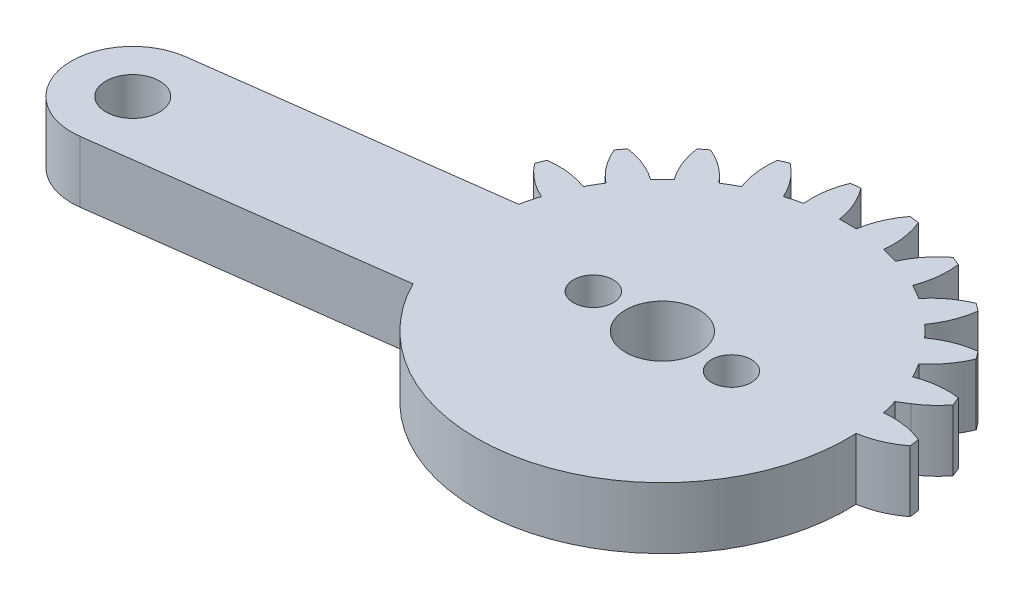
SolidWorks part; units mm, degrees
ref_plane "Front Plane" through (0, 0, 0) normal (0, 0, 1) x (1, 0, 0)
ref_plane "Top Plane" through (0, 0, 0) normal (0, 1, 0) x (1, 0, 0)
ref_plane "Right Plane" through (0, 0, 0) normal (1, 0, 0) x (0, 0, -1)
sketch "Sketch1" plane through (0, 0, 0) normal (0, 1, 0) x (1, 0, 0)
  line L0 (20.6437, 4) -> (2.0816, 4)
  line L1 (2.0816, -4) -> (20.6437, -4)
  arc A0 (2.0816, 4) -> (3.5217, 5.3071) centre (-0.7683, 8.5867) ccw
  arc A1 (3.5217, 5.3071) -> (3.2829, 5.8838) centre (-10.1063, 0) ccw
  arc A2 (3.2829, 5.8838) -> (0.6271, 5.5703) centre (2.5684, 0.5313) ccw
  arc A3 (0.6271, 5.5703) -> (0.0844, 6.5103) centre (-10.1063, 0) ccw
  arc A4 (0.0844, 6.5103) -> (1.6838, 8.6535) centre (-3.3089, 10.711) ccw
  arc A5 (1.6838, 8.6535) -> (1.3038, 9.1487) centre (-10.1063, 0) ccw
  arc A6 (1.3038, 9.1487) -> (-1.1803, 8.1585) centre (1.999, 3.7936) ccw
  arc A7 (-1.1803, 8.1585) -> (-1.9479, 8.926) centre (-10.1063, 0) ccw
  arc A8 (-1.9479, 8.926) -> (-0.9576, 11.4102) centre (-6.3127, 12.1053) ccw
  arc A9 (-0.9576, 11.4102) -> (-1.4528, 11.7901) centre (-10.1063, 0) ccw
  arc A10 (-1.4528, 11.7901) -> (-3.596, 10.1907) centre (0.6046, 6.7975) ccw
  arc A11 (-3.596, 10.1907) -> (-4.5361, 10.7334) centre (-10.1063, 0) ccw
  arc A12 (-4.5361, 10.7334) -> (-4.2225, 13.3892) centre (-9.5751, 12.6747) ccw
  arc A13 (-4.2225, 13.3892) -> (-4.7992, 13.6281) centre (-10.1063, 0) ccw
  arc A14 (-4.7992, 13.6281) -> (-6.4554, 11.5285) centre (-1.5196, 9.3381) ccw
  arc A15 (-6.4554, 11.5285) -> (-7.5039, 11.8094) centre (-10.1063, 0) ccw
  arc A16 (-7.5039, 11.8094) -> (-7.8884, 14.4558) centre (-12.8736, 12.3803) ccw
  arc A17 (-7.8884, 14.4558) -> (-8.5072, 14.5373) centre (-10.1063, 0) ccw
  arc A18 (-8.5072, 14.5373) -> (-9.5636, 12.0806) centre (-4.2291, 11.2423) ccw
  arc A19 (-9.5636, 12.0806) -> (-10.6491, 12.0806) centre (-10.1063, 0) ccw
  arc A20 (-10.6491, 12.0806) -> (-11.7054, 14.5373) centre (-15.9836, 11.2423) ccw
  arc A21 (-11.7054, 14.5373) -> (-12.3243, 14.4558) centre (-10.1063, 0) ccw
  arc A22 (-12.3243, 14.4558) -> (-12.7088, 11.8094) centre (-7.3391, 12.3803) ccw
  arc A23 (-12.7088, 11.8094) -> (-13.7573, 11.5285) centre (-10.1063, 0) ccw
  arc A24 (-13.7573, 11.5285) -> (-15.4135, 13.6281) centre (-18.6931, 9.3381) ccw
  arc A25 (-15.4135, 13.6281) -> (-15.9901, 13.3892) centre (-10.1063, 0) ccw
  arc A26 (-15.9901, 13.3892) -> (-15.6766, 10.7334) centre (-10.6376, 12.6747) ccw
  arc A27 (-15.6766, 10.7334) -> (-16.6166, 10.1907) centre (-10.1063, 0) ccw
  arc A28 (-16.6166, 10.1907) -> (-18.7599, 11.7901) centre (-20.8173, 6.7975) ccw
  arc A29 (-18.7599, 11.7901) -> (-19.255, 11.4102) centre (-10.1063, 0) ccw
  arc A30 (-19.255, 11.4102) -> (-18.2648, 8.926) centre (-13.9, 12.1053) ccw
  arc A31 (-18.2648, 8.926) -> (-19.0324, 8.1585) centre (-10.1063, 0) ccw
  arc A32 (-19.0324, 8.1585) -> (-21.5165, 9.1487) centre (-22.2117, 3.7936) ccw
  arc A33 (-21.5165, 9.1487) -> (-21.8965, 8.6535) centre (-10.1063, 0) ccw
  arc A34 (-21.8965, 8.6535) -> (-20.2971, 6.5103) centre (-16.9038, 10.711) ccw
  arc A35 (-20.2971, 6.5103) -> (-20.8398, 5.5703) centre (-10.1063, 0) ccw
  arc A36 (-20.8398, 5.5703) -> (-23.4956, 5.8838) centre (-22.7811, 0.5313) ccw
  arc A37 (-23.4956, 5.8838) -> (-23.7344, 5.3071) centre (-10.1063, 0) ccw
  arc A38 (-23.7344, 5.3071) -> (-21.6348, 3.6509) centre (-19.4444, 8.5867) ccw
  arc A39 (-21.6348, 3.6509) -> (-21.9157, 2.6025) centre (-10.1063, 0) ccw
  arc A40 (-21.9157, 2.6025) -> (-24.5622, 2.2179) centre (-22.4867, -2.7673) ccw
  arc A41 (-24.5622, 2.2179) -> (-24.6437, 1.5991) centre (-10.1063, 0) ccw
  arc A42 (-24.6437, 1.5991) -> (-22.1869, 0.5427) centre (-21.3486, 5.8773) ccw
  arc A43 (-22.1869, 0.5427) -> (-22.1869, -0.5427) centre (-10.1063, 0) ccw
  arc A44 (-22.1869, -0.5427) -> (-24.6437, -1.5991) centre (-21.3486, -5.8773) ccw
  arc A45 (-24.6437, -1.5991) -> (-24.5622, -2.2179) centre (-10.1063, 0) ccw
  arc A46 (-24.5622, -2.2179) -> (-21.9157, -2.6025) centre (-22.4867, 2.7673) ccw
  arc A47 (-21.9157, -2.6025) -> (-21.6348, -3.6509) centre (-10.1063, 0) ccw
  arc A48 (-21.6348, -3.6509) -> (-23.7344, -5.3071) centre (-19.4444, -8.5867) ccw
  arc A49 (-23.7344, -5.3071) -> (-23.4956, -5.8838) centre (-10.1063, 0) ccw
  arc A50 (-23.4956, -5.8838) -> (-20.8398, -5.5703) centre (-22.7811, -0.5313) ccw
  arc A51 (-20.8398, -5.5703) -> (-20.2971, -6.5103) centre (-10.1063, 0) ccw
  arc A52 (-20.2971, -6.5103) -> (-21.8965, -8.6535) centre (-16.9038, -10.711) ccw
  arc A53 (-21.8965, -8.6535) -> (-21.5165, -9.1487) centre (-10.1063, 0) ccw
  arc A54 (-21.5165, -9.1487) -> (-19.0324, -8.1585) centre (-22.2117, -3.7936) ccw
  arc A55 (-19.0324, -8.1585) -> (-18.2648, -8.926) centre (-10.1063, 0) ccw
  arc A56 (-18.2648, -8.926) -> (-19.255, -11.4102) centre (-13.9, -12.1053) ccw
  arc A57 (-19.255, -11.4102) -> (-18.7599, -11.7901) centre (-10.1063, 0) ccw
  arc A58 (-18.7599, -11.7901) -> (-16.6166, -10.1907) centre (-20.8173, -6.7975) ccw
  arc A59 (-16.6166, -10.1907) -> (-15.6766, -10.7334) centre (-10.1063, 0) ccw
  arc A60 (-15.6766, -10.7334) -> (-15.9901, -13.3892) centre (-10.6376, -12.6747) ccw
  arc A61 (-15.9901, -13.3892) -> (-15.4135, -13.6281) centre (-10.1063, 0) ccw
  arc A62 (-15.4135, -13.6281) -> (-13.7573, -11.5285) centre (-18.6931, -9.3381) ccw
  arc A63 (-13.7573, -11.5285) -> (-12.7088, -11.8094) centre (-10.1063, 0) ccw
  arc A64 (-12.7088, -11.8094) -> (-12.3243, -14.4558) centre (-7.3391, -12.3803) ccw
  arc A65 (-12.3243, -14.4558) -> (-11.7054, -14.5373) centre (-10.1063, 0) ccw
  arc A66 (-11.7054, -14.5373) -> (-10.6491, -12.0806) centre (-15.9836, -11.2423) ccw
  arc A67 (-10.6491, -12.0806) -> (-9.5636, -12.0806) centre (-10.1063, 0) ccw
  arc A68 (-9.5636, -12.0806) -> (-8.5072, -14.5373) centre (-4.2291, -11.2423) ccw
  arc A69 (-8.5072, -14.5373) -> (-7.8884, -14.4558) centre (-10.1063, 0) ccw
  arc A70 (-7.8884, -14.4558) -> (-7.5039, -11.8094) centre (-12.8736, -12.3803) ccw
  arc A71 (-7.5039, -11.8094) -> (-6.4554, -11.5285) centre (-10.1063, 0) ccw
  arc A72 (-6.4554, -11.5285) -> (-4.7992, -13.6281) centre (-1.5196, -9.3381) ccw
  arc A73 (-4.7992, -13.6281) -> (-4.2225, -13.3892) centre (-10.1063, 0) ccw
  arc A74 (-4.2225, -13.3892) -> (-4.5361, -10.7334) centre (-9.5751, -12.6747) ccw
  arc A75 (-4.5361, -10.7334) -> (-3.596, -10.1907) centre (-10.1063, 0) ccw
  arc A76 (-3.596, -10.1907) -> (-1.4528, -11.7901) centre (0.6046, -6.7975) ccw
  arc A77 (-1.4528, -11.7901) -> (-0.9576, -11.4102) centre (-10.1063, 0) ccw
  arc A78 (-0.9576, -11.4102) -> (-1.9479, -8.926) centre (-6.3127, -12.1053) ccw
  arc A79 (-1.9479, -8.926) -> (-1.1803, -8.1585) centre (-10.1063, 0) ccw
  arc A80 (-1.1803, -8.1585) -> (1.3038, -9.1487) centre (1.999, -3.7936) ccw
  arc A81 (1.3038, -9.1487) -> (1.6838, -8.6535) centre (-10.1063, 0) ccw
  arc A82 (1.6838, -8.6535) -> (0.0844, -6.5103) centre (-3.3089, -10.711) ccw
  arc A83 (0.0844, -6.5103) -> (0.6271, -5.5703) centre (-10.1063, 0) ccw
  arc A84 (0.6271, -5.5703) -> (3.2829, -5.8838) centre (2.5684, -0.5313) ccw
  arc A85 (3.2829, -5.8838) -> (3.5217, -5.3071) centre (-10.1063, 0) ccw
  arc A86 (3.5217, -5.3071) -> (2.0816, -4) centre (-0.7683, -8.5867) ccw
  arc A87 (20.6437, -4) -> (20.6437, 4) centre (20.6437, 0) ccw
  circle A88 centre (-10.1063, 0) radius 1.5
  circle A89 centre (20.6437, 0) radius 1.5
  dimension "D1" = 3
  dimension "D2" = 3
extrude "Boss-Extrude1" add sketch "Sketch1" along normal blind 4
sketch "Sketch3" plane through (0, 4, 0) normal (0, 1, 0) x (1, 0, 0)
  line L0 (-10.1063, 0) -> (-40.8563, 0) construction
  line L1 (-10.1063, 0) -> (-40.5933, -4.0137)
  line L2 (-10.6284, 3.9658) -> (-41.1154, -0.0479)
  line L3 (-9.5842, -3.9658) -> (-40.0712, -7.9795)
  line L4 (-10.1063, 0) -> (-4.5096, 13.5117) construction
  line L5 (-10.1063, 0) -> (-8.1974, 14.4999) construction
  circle A0 centre (-10.1063, 0) radius 1.5
  circle A1 centre (20.6437, 0) radius 1.5 construction
  circle A2 centre (20.6437, 0) radius 1.5
  circle A3 centre (-40.5933, -4.0137) radius 1.75
  circle A4 centre (-40.5933, -4.0137) radius 4
  circle A5 centre (-10.1063, 0) radius 4
  arc A6 (-4.2225, 13.3892) -> (-4.7992, 13.6281) centre (-10.1063, 0) ccw construction
  arc A7 (-7.8884, 14.4558) -> (-8.5072, 14.5373) centre (-10.1063, 0) ccw construction
  dimension "D2" = 3
  dimension "D5" = 3.5
  dimension "D6" = 8
  dimension "D7" = 8
  dimension "D1" = 30.75
  dimension "D4" = 7.5
extrude "Boss-Extrude2" add sketch "Sketch3" against normal blind 4
sketch "Sketch4" plane through (0, 4, 0) normal (0, 1, 0) x (1, 0, 0)
  line L0 (20.6437, 4) -> (2.0816, 4) construction
  line L1 (2.0816, -4) -> (20.6437, -4) construction
  line L2 (20.6437, 4) -> (2.0816, 4)
  line L3 (2.0816, -4) -> (20.6437, -4)
  line L4 (2.0816, 4) -> (1.4381, 3.6001)
  line L5 (-21.6245, -5.5509) -> (-20.8986, -5.4553)
  line L6 (-10.1063, 0) -> (0.0844, 6.5103) construction
  line L7 (-10.1063, 0) -> (1.9742, 0.5427) construction
  line L8 (-24.5755, 2.1296) -> (-41.1154, -0.0479)
  line L9 (-40.0712, -7.9795) -> (-23.5312, -5.8019)
  line L10 (2.0816, -4) -> (20.6437, -4)
  line L11 (20.6437, 4) -> (2.0816, 4)
  line L12 (-21.9429, 2.4762) -> (-41.1154, -0.0479)
  line L13 (-40.0712, -7.9795) -> (-21.6245, -5.5509)
  line L14 (2.0816, -4) -> (20.6437, -4)
  line L15 (20.6437, 4) -> (2.0816, 4)
  circle A0 centre (-10.1063, 0) radius 12.0927
  arc A1 (3.2829, 5.8838) -> (0.6271, 5.5703) centre (2.5684, 0.5313) ccw construction
  arc A2 (3.5217, 5.3071) -> (3.2829, 5.8838) centre (-10.1063, 0) ccw construction
  arc A3 (2.0816, 4) -> (3.5217, 5.3071) centre (-0.7683, 8.5867) ccw construction
  arc A4 (20.6437, -4) -> (20.6437, 4) centre (20.6437, 0) ccw construction
  arc A5 (3.5217, -5.3071) -> (2.0816, -4) centre (-0.7683, -8.5867) ccw construction
  arc A6 (3.2829, -5.8838) -> (3.5217, -5.3071) centre (-10.1063, 0) ccw construction
  arc A7 (0.6271, -5.5703) -> (3.2829, -5.8838) centre (2.5684, -0.5313) ccw construction
  arc A8 (3.2829, 5.8838) -> (0.6271, 5.5703) centre (2.5684, 0.5313) ccw
  arc A9 (3.5217, 5.3071) -> (3.2829, 5.8838) centre (-10.1063, 0) ccw
  arc A10 (2.0816, 4) -> (3.5217, 5.3071) centre (-0.7683, 8.5867) ccw
  arc A11 (20.6437, -4) -> (20.6437, 4) centre (20.6437, 0) ccw
  arc A12 (3.5217, -5.3071) -> (2.0816, -4) centre (-0.7683, -8.5867) ccw
  arc A13 (3.2829, -5.8838) -> (3.5217, -5.3071) centre (-10.1063, 0) ccw
  arc A14 (0.6271, -5.5703) -> (3.2829, -5.8838) centre (2.5684, -0.5313) ccw
  arc A15 (1.9742, 0.5427) -> (4.431, 1.5991) centre (1.1359, 5.8773) ccw
  arc A16 (4.3495, 2.2179) -> (1.7031, 2.6025) centre (2.274, -2.7673) ccw
  arc A17 (4.431, 1.5991) -> (4.3495, 2.2179) centre (-10.1063, 0) ccw
  arc A95 (-21.6348, 3.6509) -> (-21.9157, 2.6025) centre (-10.1063, 0) ccw
  arc A96 (-41.1154, -0.0479) -> (-40.0712, -7.9795) centre (-40.5933, -4.0137) ccw
  arc A97 (-20.2971, -6.5103) -> (-21.8965, -8.6535) centre (-16.9038, -10.711) ccw
  arc A98 (-21.8965, -8.6535) -> (-21.5165, -9.1487) centre (-10.1063, 0) ccw
  arc A99 (-21.5165, -9.1487) -> (-19.0324, -8.1585) centre (-22.2117, -3.7936) ccw
  arc A100 (-19.0324, -8.1585) -> (-18.2648, -8.926) centre (-10.1063, 0) ccw
  arc A101 (-18.2648, -8.926) -> (-19.255, -11.4102) centre (-13.9, -12.1053) ccw
  arc A102 (-19.255, -11.4102) -> (-18.7599, -11.7901) centre (-10.1063, 0) ccw
  arc A103 (-18.7599, -11.7901) -> (-16.6166, -10.1907) centre (-20.8173, -6.7975) ccw
  arc A104 (-16.6166, -10.1907) -> (-15.6766, -10.7334) centre (-10.1063, 0) ccw
  arc A105 (-15.6766, -10.7334) -> (-15.9901, -13.3892) centre (-10.6376, -12.6747) ccw
  arc A106 (-15.9901, -13.3892) -> (-15.4135, -13.6281) centre (-10.1063, 0) ccw
  arc A107 (-15.4135, -13.6281) -> (-13.7573, -11.5285) centre (-18.6931, -9.3381) ccw
  arc A108 (-13.7573, -11.5285) -> (-12.7088, -11.8094) centre (-10.1063, 0) ccw
  arc A109 (-12.7088, -11.8094) -> (-12.3243, -14.4558) centre (-7.3391, -12.3803) ccw
  arc A110 (-12.3243, -14.4558) -> (-11.7054, -14.5373) centre (-10.1063, 0) ccw
  arc A111 (-11.7054, -14.5373) -> (-10.6491, -12.0806) centre (-15.9836, -11.2423) ccw
  arc A112 (-10.6491, -12.0806) -> (-9.5636, -12.0806) centre (-10.1063, 0) ccw
  arc A113 (-9.5636, -12.0806) -> (-8.5072, -14.5373) centre (-4.2291, -11.2423) ccw
  arc A114 (-8.5072, -14.5373) -> (-7.8884, -14.4558) centre (-10.1063, 0) ccw
  arc A115 (-7.8884, -14.4558) -> (-7.5039, -11.8094) centre (-12.8736, -12.3803) ccw
  arc A116 (-7.5039, -11.8094) -> (-6.4554, -11.5285) centre (-10.1063, 0) ccw
  arc A117 (-6.4554, -11.5285) -> (-4.7992, -13.6281) centre (-1.5196, -9.3381) ccw
  arc A118 (-4.7992, -13.6281) -> (-4.2225, -13.3892) centre (-10.1063, 0) ccw
  arc A119 (-4.2225, -13.3892) -> (-4.5361, -10.7334) centre (-9.5751, -12.6747) ccw
  arc A120 (-4.5361, -10.7334) -> (-3.596, -10.1907) centre (-10.1063, 0) ccw
  arc A121 (-3.596, -10.1907) -> (-1.4528, -11.7901) centre (0.6046, -6.7975) ccw
  arc A122 (-1.4528, -11.7901) -> (-0.9576, -11.4102) centre (-10.1063, 0) ccw
  arc A123 (-0.9576, -11.4102) -> (-1.9479, -8.926) centre (-6.3127, -12.1053) ccw
  arc A124 (-1.9479, -8.926) -> (-1.1803, -8.1585) centre (-10.1063, 0) ccw
  arc A125 (-1.1803, -8.1585) -> (1.3038, -9.1487) centre (1.999, -3.7936) ccw
  arc A126 (1.3038, -9.1487) -> (1.6838, -8.6535) centre (-10.1063, 0) ccw
  arc A127 (1.6838, -8.6535) -> (0.0844, -6.5103) centre (-3.3089, -10.711) ccw
  arc A128 (0.0844, -6.5103) -> (0.6271, -5.5703) centre (-10.1063, 0) ccw
  arc A129 (0.6271, -5.5703) -> (3.2829, -5.8838) centre (2.5684, -0.5313) ccw
  arc A130 (3.2829, -5.8838) -> (3.5217, -5.3071) centre (-10.1063, 0) ccw
  arc A131 (3.5217, -5.3071) -> (2.0816, -4) centre (-0.7683, -8.5867) ccw
  arc A132 (20.6437, -4) -> (20.6437, 4) centre (20.6437, 0) ccw
  arc A133 (2.0816, 4) -> (3.5217, 5.3071) centre (-0.7683, 8.5867) ccw
  arc A134 (3.5217, 5.3071) -> (3.2829, 5.8838) centre (-10.1063, 0) ccw
  arc A135 (3.2829, 5.8838) -> (0.6271, 5.5703) centre (2.5684, 0.5313) ccw
  arc A136 (0.6271, 5.5703) -> (0.0844, 6.5103) centre (-10.1063, 0) ccw
  arc A137 (0.0844, 6.5103) -> (1.6838, 8.6535) centre (-3.3089, 10.711) ccw
  arc A138 (1.6838, 8.6535) -> (1.3038, 9.1487) centre (-10.1063, 0) ccw
  arc A139 (1.3038, 9.1487) -> (-1.1803, 8.1585) centre (1.999, 3.7936) ccw
  arc A140 (-1.1803, 8.1585) -> (-1.9479, 8.926) centre (-10.1063, 0) ccw
  arc A141 (-1.9479, 8.926) -> (-0.9576, 11.4102) centre (-6.3127, 12.1053) ccw
  arc A142 (-0.9576, 11.4102) -> (-1.4528, 11.7901) centre (-10.1063, 0) ccw
  arc A143 (-1.4528, 11.7901) -> (-3.596, 10.1907) centre (0.6046, 6.7975) ccw
  arc A144 (-3.596, 10.1907) -> (-4.5361, 10.7334) centre (-10.1063, 0) ccw
  arc A145 (-4.5361, 10.7334) -> (-4.2225, 13.3892) centre (-9.5751, 12.6747) ccw
  arc A146 (-4.2225, 13.3892) -> (-4.7992, 13.6281) centre (-10.1063, 0) ccw
  arc A147 (-4.7992, 13.6281) -> (-6.4554, 11.5285) centre (-1.5196, 9.3381) ccw
  arc A148 (-6.4554, 11.5285) -> (-7.5039, 11.8094) centre (-10.1063, 0) ccw
  arc A149 (-7.5039, 11.8094) -> (-7.8884, 14.4558) centre (-12.8736, 12.3803) ccw
  arc A150 (-7.8884, 14.4558) -> (-8.5072, 14.5373) centre (-10.1063, 0) ccw
  arc A151 (-8.5072, 14.5373) -> (-9.5636, 12.0806) centre (-4.2291, 11.2423) ccw
  arc A152 (-9.5636, 12.0806) -> (-10.6491, 12.0806) centre (-10.1063, 0) ccw
  arc A153 (-10.6491, 12.0806) -> (-11.7054, 14.5373) centre (-15.9836, 11.2423) ccw
  arc A154 (-11.7054, 14.5373) -> (-12.3243, 14.4558) centre (-10.1063, 0) ccw
  arc A155 (-12.3243, 14.4558) -> (-12.7088, 11.8094) centre (-7.3391, 12.3803) ccw
  arc A156 (-12.7088, 11.8094) -> (-13.7573, 11.5285) centre (-10.1063, 0) ccw
  arc A157 (-13.7573, 11.5285) -> (-15.4135, 13.6281) centre (-18.6931, 9.3381) ccw
  arc A158 (-15.4135, 13.6281) -> (-15.9901, 13.3892) centre (-10.1063, 0) ccw
  arc A159 (-15.9901, 13.3892) -> (-15.6766, 10.7334) centre (-10.6376, 12.6747) ccw
  arc A160 (-15.6766, 10.7334) -> (-16.6166, 10.1907) centre (-10.1063, 0) ccw
  arc A161 (-16.6166, 10.1907) -> (-18.7599, 11.7901) centre (-20.8173, 6.7975) ccw
  arc A162 (-18.7599, 11.7901) -> (-19.255, 11.4102) centre (-10.1063, 0) ccw
  arc A163 (-19.255, 11.4102) -> (-18.2648, 8.926) centre (-13.9, 12.1053) ccw
  arc A164 (-18.2648, 8.926) -> (-19.0324, 8.1585) centre (-10.1063, 0) ccw
  arc A165 (-19.0324, 8.1585) -> (-21.5165, 9.1487) centre (-22.2117, 3.7936) ccw
  arc A166 (-21.5165, 9.1487) -> (-21.8965, 8.6535) centre (-10.1063, 0) ccw
  arc A167 (-21.8965, 8.6535) -> (-20.2971, 6.5103) centre (-16.9038, 10.711) ccw
  arc A168 (-20.2971, 6.5103) -> (-20.8398, 5.5703) centre (-10.1063, 0) ccw
  arc A169 (-20.8398, 5.5703) -> (-23.4956, 5.8838) centre (-22.7811, 0.5313) ccw
  arc A170 (-23.4956, 5.8838) -> (-23.7344, 5.3071) centre (-10.1063, 0) ccw
  arc A171 (-23.7344, 5.3071) -> (-21.6348, 3.6509) centre (-19.4444, 8.5867) ccw
  arc A172 (-21.6348, 3.6509) -> (-21.9157, 2.6025) centre (-10.1063, 0) ccw
  arc A175 (-23.4956, -5.8838) -> (-20.8398, -5.5703) centre (-22.7811, -0.5313) ccw
  arc A176 (-41.1154, -0.0479) -> (-40.0712, -7.9795) centre (-40.5933, -4.0137) ccw
  arc A177 (-20.2971, -6.5103) -> (-21.8965, -8.6535) centre (-16.9038, -10.711) ccw
  arc A178 (-21.8965, -8.6535) -> (-21.5165, -9.1487) centre (-10.1063, 0) ccw
  arc A179 (-21.5165, -9.1487) -> (-19.0324, -8.1585) centre (-22.2117, -3.7936) ccw
  arc A180 (-19.0324, -8.1585) -> (-18.2648, -8.926) centre (-10.1063, 0) ccw
  arc A181 (-18.2648, -8.926) -> (-19.255, -11.4102) centre (-13.9, -12.1053) ccw
  arc A182 (-19.255, -11.4102) -> (-18.7599, -11.7901) centre (-10.1063, 0) ccw
  arc A183 (-18.7599, -11.7901) -> (-16.6166, -10.1907) centre (-20.8173, -6.7975) ccw
  arc A184 (-16.6166, -10.1907) -> (-15.6766, -10.7334) centre (-10.1063, 0) ccw
  arc A185 (-15.6766, -10.7334) -> (-15.9901, -13.3892) centre (-10.6376, -12.6747) ccw
  arc A186 (-15.9901, -13.3892) -> (-15.4135, -13.6281) centre (-10.1063, 0) ccw
  arc A187 (-15.4135, -13.6281) -> (-13.7573, -11.5285) centre (-18.6931, -9.3381) ccw
  arc A188 (-13.7573, -11.5285) -> (-12.7088, -11.8094) centre (-10.1063, 0) ccw
  arc A189 (-12.7088, -11.8094) -> (-12.3243, -14.4558) centre (-7.3391, -12.3803) ccw
  arc A190 (-12.3243, -14.4558) -> (-11.7054, -14.5373) centre (-10.1063, 0) ccw
  arc A191 (-11.7054, -14.5373) -> (-10.6491, -12.0806) centre (-15.9836, -11.2423) ccw
  arc A192 (-10.6491, -12.0806) -> (-9.5636, -12.0806) centre (-10.1063, 0) ccw
  arc A193 (-9.5636, -12.0806) -> (-8.5072, -14.5373) centre (-4.2291, -11.2423) ccw
  arc A194 (-8.5072, -14.5373) -> (-7.8884, -14.4558) centre (-10.1063, 0) ccw
  arc A195 (-7.8884, -14.4558) -> (-7.5039, -11.8094) centre (-12.8736, -12.3803) ccw
  arc A196 (-7.5039, -11.8094) -> (-6.4554, -11.5285) centre (-10.1063, 0) ccw
  arc A197 (-6.4554, -11.5285) -> (-4.7992, -13.6281) centre (-1.5196, -9.3381) ccw
  arc A198 (-4.7992, -13.6281) -> (-4.2225, -13.3892) centre (-10.1063, 0) ccw
  arc A199 (-4.2225, -13.3892) -> (-4.5361, -10.7334) centre (-9.5751, -12.6747) ccw
  arc A200 (-4.5361, -10.7334) -> (-3.596, -10.1907) centre (-10.1063, 0) ccw
  arc A201 (-3.596, -10.1907) -> (-1.4528, -11.7901) centre (0.6046, -6.7975) ccw
  arc A202 (-1.4528, -11.7901) -> (-0.9576, -11.4102) centre (-10.1063, 0) ccw
  arc A203 (-0.9576, -11.4102) -> (-1.9479, -8.926) centre (-6.3127, -12.1053) ccw
  arc A204 (-1.9479, -8.926) -> (-1.1803, -8.1585) centre (-10.1063, 0) ccw
  arc A205 (-1.1803, -8.1585) -> (1.3038, -9.1487) centre (1.999, -3.7936) ccw
  arc A206 (1.3038, -9.1487) -> (1.6838, -8.6535) centre (-10.1063, 0) ccw
  arc A207 (1.6838, -8.6535) -> (0.0844, -6.5103) centre (-3.3089, -10.711) ccw
  arc A208 (0.0844, -6.5103) -> (0.6271, -5.5703) centre (-10.1063, 0) ccw
  arc A209 (0.6271, -5.5703) -> (3.2829, -5.8838) centre (2.5684, -0.5313) ccw
  arc A210 (3.2829, -5.8838) -> (3.5217, -5.3071) centre (-10.1063, 0) ccw
  arc A211 (3.5217, -5.3071) -> (2.0816, -4) centre (-0.7683, -8.5867) ccw
  arc A212 (20.6437, -4) -> (20.6437, 4) centre (20.6437, 0) ccw
  arc A213 (2.0816, 4) -> (3.5217, 5.3071) centre (-0.7683, 8.5867) ccw
  arc A214 (3.5217, 5.3071) -> (3.2829, 5.8838) centre (-10.1063, 0) ccw
  arc A215 (3.2829, 5.8838) -> (0.6271, 5.5703) centre (2.5684, 0.5313) ccw
  arc A216 (0.6271, 5.5703) -> (0.0844, 6.5103) centre (-10.1063, 0) ccw
  arc A217 (0.0844, 6.5103) -> (1.6838, 8.6535) centre (-3.3089, 10.711) ccw
  arc A218 (1.6838, 8.6535) -> (1.3038, 9.1487) centre (-10.1063, 0) ccw
  arc A219 (1.3038, 9.1487) -> (-1.1803, 8.1585) centre (1.999, 3.7936) ccw
  arc A220 (-1.1803, 8.1585) -> (-1.9479, 8.926) centre (-10.1063, 0) ccw
  arc A221 (-1.9479, 8.926) -> (-0.9576, 11.4102) centre (-6.3127, 12.1053) ccw
  arc A222 (-0.9576, 11.4102) -> (-1.4528, 11.7901) centre (-10.1063, 0) ccw
  arc A223 (-1.4528, 11.7901) -> (-3.596, 10.1907) centre (0.6046, 6.7975) ccw
  arc A224 (-3.596, 10.1907) -> (-4.5361, 10.7334) centre (-10.1063, 0) ccw
  arc A225 (-4.5361, 10.7334) -> (-4.2225, 13.3892) centre (-9.5751, 12.6747) ccw
  arc A226 (-4.2225, 13.3892) -> (-4.7992, 13.6281) centre (-10.1063, 0) ccw
  arc A227 (-4.7992, 13.6281) -> (-6.4554, 11.5285) centre (-1.5196, 9.3381) ccw
  arc A228 (-6.4554, 11.5285) -> (-7.5039, 11.8094) centre (-10.1063, 0) ccw
  arc A229 (-7.5039, 11.8094) -> (-7.8884, 14.4558) centre (-12.8736, 12.3803) ccw
  arc A230 (-7.8884, 14.4558) -> (-8.5072, 14.5373) centre (-10.1063, 0) ccw
  arc A231 (-8.5072, 14.5373) -> (-9.5636, 12.0806) centre (-4.2291, 11.2423) ccw
  arc A232 (-9.5636, 12.0806) -> (-10.6491, 12.0806) centre (-10.1063, 0) ccw
  arc A233 (-10.6491, 12.0806) -> (-11.7054, 14.5373) centre (-15.9836, 11.2423) ccw
  arc A234 (-11.7054, 14.5373) -> (-12.3243, 14.4558) centre (-10.1063, 0) ccw
  arc A235 (-12.3243, 14.4558) -> (-12.7088, 11.8094) centre (-7.3391, 12.3803) ccw
  arc A236 (-12.7088, 11.8094) -> (-13.7573, 11.5285) centre (-10.1063, 0) ccw
  arc A237 (-13.7573, 11.5285) -> (-15.4135, 13.6281) centre (-18.6931, 9.3381) ccw
  arc A238 (-15.4135, 13.6281) -> (-15.9901, 13.3892) centre (-10.1063, 0) ccw
  arc A239 (-15.9901, 13.3892) -> (-15.6766, 10.7334) centre (-10.6376, 12.6747) ccw
  arc A240 (-15.6766, 10.7334) -> (-16.6166, 10.1907) centre (-10.1063, 0) ccw
  arc A241 (-16.6166, 10.1907) -> (-18.7599, 11.7901) centre (-20.8173, 6.7975) ccw
  arc A242 (-18.7599, 11.7901) -> (-19.255, 11.4102) centre (-10.1063, 0) ccw
  arc A243 (-19.255, 11.4102) -> (-18.2648, 8.926) centre (-13.9, 12.1053) ccw
  arc A244 (-18.2648, 8.926) -> (-19.0324, 8.1585) centre (-10.1063, 0) ccw
  arc A245 (-19.0324, 8.1585) -> (-21.5165, 9.1487) centre (-22.2117, 3.7936) ccw
  arc A246 (-21.5165, 9.1487) -> (-21.8965, 8.6535) centre (-10.1063, 0) ccw
  arc A247 (-21.8965, 8.6535) -> (-20.2971, 6.5103) centre (-16.9038, 10.711) ccw
  arc A248 (-20.2971, 6.5103) -> (-20.8398, 5.5703) centre (-10.1063, 0) ccw
  arc A249 (-20.8398, 5.5703) -> (-23.4956, 5.8838) centre (-22.7811, 0.5313) ccw
  arc A250 (-23.4956, 5.8838) -> (-23.7344, 5.3071) centre (-10.1063, 0) ccw
  arc A251 (-23.7344, 5.3071) -> (-21.6348, 3.6509) centre (-19.4444, 8.5867) ccw
  arc A252 (-23.4956, -5.8838) -> (-20.8398, -5.5703) centre (-22.7811, -0.5313) ccw
  arc A253 (-20.8398, -5.5703) -> (-20.2971, -6.5103) centre (-10.1063, 0) ccw
  arc A254 (-20.8398, -5.5703) -> (-20.2971, -6.5103) centre (-10.1063, 0) ccw
  arc A255 (-23.5312, -5.8019) -> (-23.4956, -5.8838) centre (-10.1063, 0) ccw
  arc A256 (-23.5312, -5.8019) -> (-23.4956, -5.8838) centre (-10.1063, 0) ccw
  arc A257 (-21.9157, 2.6025) -> (-24.5622, 2.2179) centre (-22.4867, -2.7673) ccw
  arc A258 (-21.9157, 2.6025) -> (-24.5622, 2.2179) centre (-22.4867, -2.7673) ccw
  arc A259 (-24.5622, 2.2179) -> (-24.5755, 2.1296) centre (-10.1063, 0) ccw
  arc A260 (-24.5622, 2.2179) -> (-24.5755, 2.1296) centre (-10.1063, 0) ccw
  point P40 (-10.1063, 0)
  dimension "D2" = 24.1855
  dimension "D4" = 30
  dimension "D1" = 0
  dimension "D3" = 2
extrude "Cut-Extrude1" cut sketch "Sketch4" against normal blind 4 contours A178 A179 A0 L5 A177 | A182 A183 A0 A181 | A186 A187 A0 A185 | A190 A191 A0 A189 | A194 A195 A0 A193 | A198 A199 A0 A197 | A202 A203 A0 A201 | A206 A207 A0 A205 | A258 A260 L12 A0 | L13 A256 A252 A0 L5 | A0 A14 A13 A12 L3 A11 L2 L4
sketch "Sketch5" plane through (0, 4, 0) normal (0, 1, 0) x (1, 0, 0)
  circle A0 centre (-10.1063, 0) radius 2.4
  circle A1 centre (-5.6063, 0) radius 1.3
  circle A2 centre (-14.6063, 0) radius 1.3
  circle A3 centre (-10.1063, 0) radius 1.5 construction
  dimension "D1" = 4.8
  dimension "D2" = 2.6
  dimension "D3" = 2.6
  dimension "D4" = 4.5
  dimension "D5" = 9
extrude "Cut-Extrude2" cut sketch "Sketch5" against normal up to next contours A2 | A1 | A0
